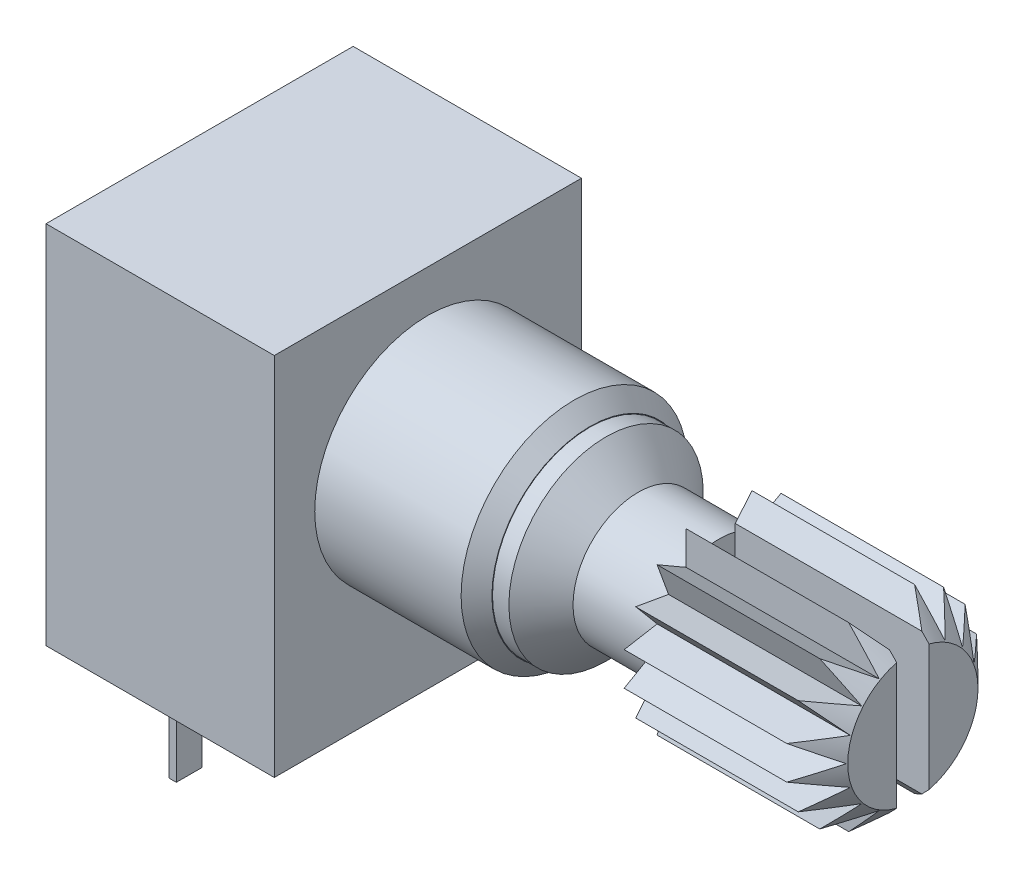
SolidWorks part; units mm, degrees
ref_plane "Front" through (0, 0, 0) normal (0, 0, 1) x (1, 0, 0)
ref_plane "Top" through (0, 0, 0) normal (0, 1, 0) x (1, 0, 0)
ref_plane "Right" through (0, 0, 0) normal (1, 0, 0) x (0, 0, -1)
ref_plane "Plane1" through (0, 0, 0) normal (0, 0, 1) x (1, 0, 0)
sketch "Sketch1" plane through (0, 0, 0) normal (0, 0, 1) x (1, 0, 0)
  line L0 (-1.5176, 0) -> (14.3895, 0) construction
  line L1 (0, 3.5) -> (4.5276, 3.5)
  line L2 (4.5276, 3.5) -> (5.0038, 3.0238)
  line L3 (5.0038, 0) -> (5.0038, 3.0238)
  line L10 (5.0038, 0) -> (0, 0)
  line L11 (0, 0) -> (0, 3.5)
  dimension "D1" = 135
  dimension "D2" = 7
  dimension "D3" = 6.0475
  dimension "D5" = 5.0038
revolve "Shaft Base" add sketch "Sketch1" angle 360 about L0
cosmetic thread "Cosmetic Thread1" parameters "D1"=5, "D2"=6.0475
sketch "Sketch8" plane through (0, 0, 0) normal (0, 0, 1) x (1, 0, 0)
  line L0 (-8.2588, 0) -> (7.6482, 0) construction
  line L1 (5.0038, 3.0059) -> (5.0038, 0)
  line L3 (5.0038, 3.0059) -> (5.5107, 3.0059)
  line L4 (5.5107, 3.0059) -> (6.5024, 2.0141)
  line L5 (6.5024, 2.0141) -> (9.0056, 2.0141)
  line L6 (9.0056, 2.0141) -> (9.0056, 2.9793)
  line L7 (9.0056, 2.9793) -> (14.0348, 2.9793)
  line L8 (14.0348, 2.9793) -> (15, 2.0141)
  line L9 (15, 2.0141) -> (15, 0)
  line L10 (15, 0) -> (5.0038, 0)
revolve "K Style Shaft" add sketch "Sketch8" angle 360 about L0
sketch "Sketch2" plane through (15, 0, 0) normal (1, 0, 0) x (0, 0, -1)
  line L0 (0, -1.9557) -> (0, 4.122) construction
  line L1 (0, 55) -> (0, -55) construction
  line L2 (0, 0) -> (1.3874, 3.8117) construction
  line L3 (0, 2.9793) -> (0.3539, 2.007)
  line L4 (0.3539, 2.007) -> (1.019, 2.7997)
  line L5 (0, 0) -> (0.791, 4.4858) construction
  line L6 (1.019, 2.7997) -> (1.019, 1.765)
  line L7 (1.019, 1.765) -> (1.9151, 2.2823)
  line L8 (1.9151, 2.2823) -> (1.5612, 1.31)
  line L9 (1.5612, 1.31) -> (2.5802, 1.4897)
  line L10 (2.5802, 1.4897) -> (1.9151, 0.697)
  line L11 (1.9151, 0.697) -> (2.9341, 0.5174)
  line L12 (2.9341, 0.5174) -> (2.038, 0)
  line L13 (2.038, 0) -> (2.9341, -0.5174)
  line L14 (2.9341, -0.5174) -> (1.9151, -0.697)
  line L15 (1.9151, -0.697) -> (2.5802, -1.4897)
  line L16 (2.5802, -1.4897) -> (1.5612, -1.31)
  line L17 (1.5612, -1.31) -> (1.9151, -2.2823)
  line L18 (1.9151, -2.2823) -> (1.019, -1.765)
  line L19 (1.019, -1.765) -> (1.019, -2.7997)
  line L20 (1.019, -2.7997) -> (0.3539, -2.007)
  line L21 (0.3539, -2.007) -> (0, -2.9793)
  line L22 (0, -2.9793) -> (-0.3539, -2.007)
  line L23 (-0.3539, -2.007) -> (-1.019, -2.7997)
  line L24 (-1.019, -2.7997) -> (-1.019, -1.765)
  line L25 (-1.019, -1.765) -> (-1.9151, -2.2823)
  line L26 (-1.9151, -2.2823) -> (-1.5612, -1.31)
  line L27 (-1.5612, -1.31) -> (-2.5802, -1.4897)
  line L28 (-2.5802, -1.4897) -> (-1.9151, -0.697)
  line L29 (-1.9151, -0.697) -> (-2.9341, -0.5174)
  line L30 (-2.9341, -0.5174) -> (-2.038, 0)
  line L31 (-2.038, 0) -> (-2.9341, 0.5174)
  line L32 (-2.9341, 0.5174) -> (-1.9151, 0.697)
  line L33 (-1.9151, 0.697) -> (-2.5802, 1.4897)
  line L34 (-2.5802, 1.4897) -> (-1.5612, 1.31)
  line L35 (-1.5612, 1.31) -> (-1.9151, 2.2823)
  line L36 (-1.9151, 2.2823) -> (-1.019, 1.765)
  line L37 (-1.019, 1.765) -> (-1.019, 2.7997)
  line L38 (-1.019, 2.7997) -> (-0.3539, 2.007)
  line L39 (-0.3539, 2.007) -> (0, 2.9793)
  circle A0 centre (0, 0) radius 2.6973 construction
  circle A1 centre (0, 0) radius 2.9793 construction
  circle A3 centre (0, 0) radius 3.8117
  circle A5 centre (0, 0) radius 2.9793 construction
  point P68 (0, 0)
  dimension "D1" = 20
  dimension "D2" = 10
  dimension "D3" = 60
  dimension "D4" = 18
extrude "18 Teeth Knurls" cut sketch "Sketch2" against normal up to surface (5.9944 mm away) up to face at (9.0056, 0, 2.0141)
sketch "Sketch3" plane through (15, 0, 0) normal (1, 0, 0) x (0, 0, -1)
  line L0 (0, -4.2748) -> (0, 4.3848) construction
  line L1 (-0.5, -3.175) -> (-0.5, 3.175)
  line L2 (0.5, 3.175) -> (0.5, -3.175)
  line L3 (-0.5, 3.175) -> (0.5, 3.175)
  line L4 (0.5, -3.175) -> (-0.5, -3.175)
  line L5 (1.0354, 0) -> (-1.0662, 0) construction
  dimension "D1" = 1
  dimension "D2" = 6.35
extrude "Cut-Extrude2" cut sketch "Sketch3" against normal up to surface (5.9944 mm away) up to face at (9.0056, 0, 2.0141)
sketch "Sketch11" [suppressed] plane through (0, 0, 0) normal (0, 0, 1) x (1, 0, 0)
  line L0 (-8.2588, 0) -> (7.6482, 0) construction
  line L1 (5.0038, 2.9972) -> (5.0038, 0)
  line L2 (5.0038, 2.9972) -> (15, 2.9972)
  line L3 (15, 2.9972) -> (15, 0)
  line L4 (15, 0) -> (5.0038, 0)
  line L5 (5.0038, -3.0238) -> (5.0038, 3.0238) construction
  dimension "D1" = 5.9944
ref_plane "Plane2" through (0, 0, 0) normal (-1, 0, 0) x (0, 0, 1)
sketch "Sketch4" plane through (0, 0, 0) normal (-1, 0, 0) x (0, 0, 1)
  line L0 (-13.9386, 0) -> (14.2421, 0) construction
  line L1 (0, -9.7766) -> (0, 15.0697) construction
  line L3 (-4.7498, -6.5024) -> (4.7498, -6.5024)
  line L4 (-4.7498, -6.5024) -> (-4.7498, 4.8006)
  line L5 (-4.7498, 4.8006) -> (4.7498, 4.8006)
  line L6 (4.7498, -6.5024) -> (4.7498, 4.8006)
  point P5 (0, 0)
  dimension "D1" = 4.8006
  dimension "D2" = 9.4996
  dimension "D3" = 6.5024
extrude "Body" add sketch "Sketch4" along normal blind 7.0612
sketch "Sketch6" plane through (0, -6.5024, 0) normal (0, -1, 0) x (1, 0, 0)
  line L0 (-8.5013, 0) -> (4.5946, 0) construction
  line L1 (-5.1143, -2.8937) -> (-4.8857, -2.8937)
  line L8 (-5.1143, -2.8937) -> (-5.1143, -2.1063)
  line L9 (-5.1143, -2.1063) -> (-4.8857, -2.1063)
  line L10 (-4.8857, -2.8937) -> (-4.8857, -2.1063)
  line L11 (-5.1143, -2.8937) -> (-4.8857, -2.1063) construction
  line L12 (-5.1143, -2.1063) -> (-4.8857, -2.8937) construction
  line L13 (0, 6.3484) -> (0, -6.1738) construction
  line L14 (-1.2923, 1.6697) -> (-1.2923, -10.8525) construction
  line L15 (-5.1143, -0.3937) -> (-4.8857, -0.3937)
  line L16 (-5.1143, -0.3937) -> (-5.1143, 0.3937)
  line L17 (-5.1143, 0.3937) -> (-4.8857, 0.3937)
  line L18 (-4.8857, -0.3937) -> (-4.8857, 0.3937)
  line L19 (-5.1143, -0.3937) -> (-4.8857, 0.3937) construction
  line L20 (-5.1143, 0.3937) -> (-4.8857, -0.3937) construction
  line L21 (-5.1143, 2.1063) -> (-4.8857, 2.1063)
  line L22 (-5.1143, 2.1063) -> (-5.1143, 2.8937)
  line L23 (-5.1143, 2.8937) -> (-4.8857, 2.8937)
  line L24 (-4.8857, 2.1063) -> (-4.8857, 2.8937)
  line L25 (-5.1143, 2.1063) -> (-4.8857, 2.8937) construction
  line L26 (-5.1143, 2.8937) -> (-4.8857, 2.1063) construction
  line L42 (0, -4.7498) -> (0, 4.7498) construction
  point P1 (-7.5, 2.5)
  point P2 (-7.5, 0)
  point P6 (-5, -2.5)
  point P19 (-5, 0)
  point P24 (-5, 2.5)
  dimension "D1" = 0.7874
  dimension "D2" = 0.2286
  dimension "D4" = 5
  dimension "D7" = 5
extrude "Pins PTD901 (one section)" add sketch "Sketch6" along normal blind 3.5
sketch "Sketch5" plane through (0, -6.5024, 0) normal (0, -1, 0) x (1, 0, 0)
  line L0 (-11.2326, 0) -> (1.8633, 0) construction
  line L1 (-5.1143, -2.8937) -> (-4.8857, -2.8937)
  line L2 (-7.6143, -2.8937) -> (-7.3857, -2.8937)
  line L3 (-7.6143, -2.8937) -> (-7.6143, -2.1063)
  line L4 (-7.6143, -2.1063) -> (-7.3857, -2.1063)
  line L5 (-7.3857, -2.8937) -> (-7.3857, -2.1063)
  line L6 (-7.6143, -2.8937) -> (-7.3857, -2.1063) construction
  line L7 (-7.6143, -2.1063) -> (-7.3857, -2.8937) construction
  line L8 (-5.1143, -2.8937) -> (-5.1143, -2.1063)
  line L9 (-5.1143, -2.1063) -> (-4.8857, -2.1063)
  line L10 (-4.8857, -2.8937) -> (-4.8857, -2.1063)
  line L11 (-5.1143, -2.8937) -> (-4.8857, -2.1063) construction
  line L12 (-5.1143, -2.1063) -> (-4.8857, -2.8937) construction
  line L13 (0, 6.3484) -> (0, -6.1738) construction
  line L14 (-4.0236, 6.3484) -> (-4.0236, -6.1738) construction
  line L15 (-5.1143, -0.3937) -> (-4.8857, -0.3937)
  line L16 (-5.1143, -0.3937) -> (-5.1143, 0.3937)
  line L17 (-5.1143, 0.3937) -> (-4.8857, 0.3937)
  line L18 (-4.8857, -0.3937) -> (-4.8857, 0.3937)
  line L19 (-5.1143, -0.3937) -> (-4.8857, 0.3937) construction
  line L20 (-5.1143, 0.3937) -> (-4.8857, -0.3937) construction
  line L21 (-5.1143, 2.1063) -> (-4.8857, 2.1063)
  line L22 (-5.1143, 2.1063) -> (-5.1143, 2.8937)
  line L23 (-5.1143, 2.8937) -> (-4.8857, 2.8937)
  line L24 (-4.8857, 2.1063) -> (-4.8857, 2.8937)
  line L25 (-5.1143, 2.1063) -> (-4.8857, 2.8937) construction
  line L26 (-5.1143, 2.8937) -> (-4.8857, 2.1063) construction
  line L27 (-7.6143, -0.3937) -> (-7.3857, -0.3937)
  line L28 (-7.6143, -0.3937) -> (-7.6143, 0.3937)
  line L29 (-7.6143, 0.3937) -> (-7.3857, 0.3937)
  line L30 (-7.3857, -0.3937) -> (-7.3857, 0.3937)
  line L31 (-7.6143, -0.3937) -> (-7.3857, 0.3937) construction
  line L32 (-7.6143, 0.3937) -> (-7.3857, -0.3937) construction
  line L33 (-7.6143, 2.1063) -> (-7.3857, 2.1063)
  line L34 (-7.6143, 2.1063) -> (-7.6143, 2.8937)
  line L35 (-7.6143, 2.8937) -> (-7.3857, 2.8937)
  line L36 (-7.3857, 2.1063) -> (-7.3857, 2.8937)
  line L37 (-7.6143, 2.1063) -> (-7.3857, 2.8937) construction
  line L38 (-7.6143, 2.8937) -> (-7.3857, 2.1063) construction
  point P0 (-7.5, -2.5)
  point P6 (-5, -2.5)
  point P19 (-5, 0)
  point P24 (-5, 2.5)
  point P29 (-7.5, 0)
  point P34 (-7.5, 2.5)
  dimension "D1" = 0.7874
  dimension "D2" = 0.2286
  dimension "D3" = 2.5
  dimension "D4" = 5
  dimension "D5" = 2
  dimension "D7" = 5
  dimension "D8" = 2.5
  dimension "D6" = 3
sketch "Sketch7" [suppressed] plane through (0, -6.5024, 0) normal (0, -1, 0) x (1, 0, 0)
  line L0 (-7.4573, 0) -> (5.6387, 0) construction
  line L1 (-5.1143, -2.8937) -> (-4.8857, -2.8937)
  line L2 (-7.6143, -2.8937) -> (-7.3857, -2.8937)
  line L3 (-7.6143, -2.8937) -> (-7.6143, -2.1063)
  line L4 (-7.6143, -2.1063) -> (-7.3857, -2.1063)
  line L5 (-7.3857, -2.8937) -> (-7.3857, -2.1063)
  line L6 (-7.6143, -2.8937) -> (-7.3857, -2.1063) construction
  line L7 (-7.6143, -2.1063) -> (-7.3857, -2.8937) construction
  line L8 (-5.1143, -2.8937) -> (-5.1143, -2.1063)
  line L9 (-5.1143, -2.1063) -> (-4.8857, -2.1063)
  line L10 (-4.8857, -2.8937) -> (-4.8857, -2.1063)
  line L11 (-5.1143, -2.8937) -> (-4.8857, -2.1063) construction
  line L12 (-5.1143, -2.1063) -> (-4.8857, -2.8937) construction
  line L13 (0, 3.2728) -> (0, -9.2494) construction
  line L14 (-0.2483, 3.2728) -> (-0.2483, -9.2494) construction
  line L15 (-5.1143, -0.3937) -> (-4.8857, -0.3937)
  line L16 (-5.1143, -0.3937) -> (-5.1143, 0.3937)
  line L17 (-5.1143, 0.3937) -> (-4.8857, 0.3937)
  line L18 (-4.8857, -0.3937) -> (-4.8857, 0.3937)
  line L19 (-5.1143, -0.3937) -> (-4.8857, 0.3937) construction
  line L20 (-5.1143, 0.3937) -> (-4.8857, -0.3937) construction
  line L21 (-5.1143, 2.1063) -> (-4.8857, 2.1063)
  line L22 (-5.1143, 2.1063) -> (-5.1143, 2.8937)
  line L23 (-5.1143, 2.8937) -> (-4.8857, 2.8937)
  line L24 (-4.8857, 2.1063) -> (-4.8857, 2.8937)
  line L25 (-5.1143, 2.1063) -> (-4.8857, 2.8937) construction
  line L26 (-5.1143, 2.8937) -> (-4.8857, 2.1063) construction
  line L27 (-7.6143, -0.3937) -> (-7.3857, -0.3937)
  line L28 (-7.6143, -0.3937) -> (-7.6143, 0.3937)
  line L29 (-7.6143, 0.3937) -> (-7.3857, 0.3937)
  line L30 (-7.3857, -0.3937) -> (-7.3857, 0.3937)
  line L31 (-7.6143, -0.3937) -> (-7.3857, 0.3937) construction
  line L32 (-7.6143, 0.3937) -> (-7.3857, -0.3937) construction
  line L33 (-7.6143, 2.1063) -> (-7.3857, 2.1063)
  line L34 (-7.6143, 2.1063) -> (-7.6143, 2.8937)
  line L35 (-7.6143, 2.8937) -> (-7.3857, 2.8937)
  line L36 (-7.3857, 2.1063) -> (-7.3857, 2.8937)
  line L37 (-7.6143, 2.1063) -> (-7.3857, 2.8937) construction
  line L38 (-7.6143, 2.8937) -> (-7.3857, 2.1063) construction
  line L39 (0, -4.7498) -> (0, 4.7498) construction
  line L40 (-12.6143, -2.8937) -> (-12.3857, -2.8937)
  line L41 (-15.1143, -2.8937) -> (-14.8857, -2.8937)
  line L42 (-15.1143, -2.8937) -> (-15.1143, -2.1063)
  line L43 (-15.1143, -2.1063) -> (-14.8857, -2.1063)
  line L44 (-14.8857, -2.8937) -> (-14.8857, -2.1063)
  line L45 (-15.1143, -2.8937) -> (-14.8857, -2.1063) construction
  line L46 (-15.1143, -2.1063) -> (-14.8857, -2.8937) construction
  line L47 (-12.6143, -2.8937) -> (-12.6143, -2.1063)
  line L48 (-12.6143, -2.1063) -> (-12.3857, -2.1063)
  line L49 (-12.3857, -2.8937) -> (-12.3857, -2.1063)
  line L50 (-12.6143, -2.8937) -> (-12.3857, -2.1063) construction
  line L51 (-12.6143, -2.1063) -> (-12.3857, -2.8937) construction
  line L52 (-12.6143, -0.3937) -> (-12.3857, -0.3937)
  line L53 (-12.6143, -0.3937) -> (-12.6143, 0.3937)
  line L54 (-12.6143, 0.3937) -> (-12.3857, 0.3937)
  line L55 (-12.3857, -0.3937) -> (-12.3857, 0.3937)
  line L56 (-12.6143, -0.3937) -> (-12.3857, 0.3937) construction
  line L57 (-12.6143, 0.3937) -> (-12.3857, -0.3937) construction
  line L58 (-12.6143, 2.1063) -> (-12.3857, 2.1063)
  line L59 (-12.6143, 2.1063) -> (-12.6143, 2.8937)
  line L60 (-12.6143, 2.8937) -> (-12.3857, 2.8937)
  line L61 (-12.3857, 2.1063) -> (-12.3857, 2.8937)
  line L62 (-12.6143, 2.1063) -> (-12.3857, 2.8937) construction
  line L63 (-12.6143, 2.8937) -> (-12.3857, 2.1063) construction
  line L64 (-15.1143, -0.3937) -> (-14.8857, -0.3937)
  line L65 (-15.1143, -0.3937) -> (-15.1143, 0.3937)
  line L66 (-15.1143, 0.3937) -> (-14.8857, 0.3937)
  line L67 (-14.8857, -0.3937) -> (-14.8857, 0.3937)
  line L68 (-15.1143, -0.3937) -> (-14.8857, 0.3937) construction
  line L69 (-15.1143, 0.3937) -> (-14.8857, -0.3937) construction
  line L70 (-15.1143, 2.1063) -> (-14.8857, 2.1063)
  line L71 (-15.1143, 2.1063) -> (-15.1143, 2.8937)
  line L72 (-15.1143, 2.8937) -> (-14.8857, 2.8937)
  line L73 (-14.8857, 2.1063) -> (-14.8857, 2.8937)
  line L74 (-15.1143, 2.1063) -> (-14.8857, 2.8937) construction
  line L75 (-15.1143, 2.8937) -> (-14.8857, 2.1063) construction
  point P0 (-7.5, -2.5)
  point P6 (-5, -2.5)
  point P19 (-5, 0)
  point P24 (-5, 2.5)
  point P29 (-7.5, 0)
  point P34 (-7.5, 2.5)
  point P40 (-15, -2.5)
  point P45 (-12.5, -2.5)
  point P50 (-12.5, 0)
  point P55 (-12.5, 2.5)
  point P60 (-15, 0)
  point P65 (-15, 2.5)
  dimension "D1" = 0.7874
  dimension "D2" = 0.2286
  dimension "D3" = 2.5
  dimension "D4" = 5
  dimension "D5" = 2
  dimension "D7" = 5
  dimension "D8" = 2.5
  dimension "D9" = 5
  dimension "D10" = 2.5
  dimension "D11" = 2.5
  dimension "D12" = 5
  dimension "D6" = 3
